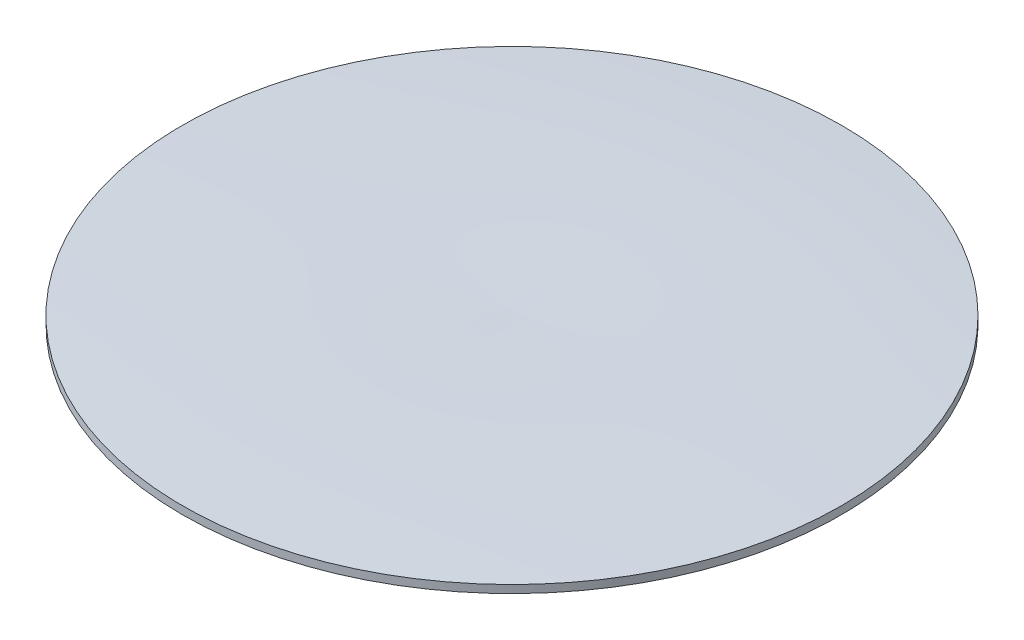
SolidWorks part; units mm, degrees
ref_plane "Front Plane" through (0, 0, 0) normal (0, 0, 1) x (1, 0, 0)
ref_plane "Top Plane" through (0, 0, 0) normal (0, 1, 0) x (1, 0, 0)
ref_plane "Right Plane" through (0, 0, 0) normal (1, 0, 0) x (0, 0, -1)
sketch "Sketch2" plane through (0, 0, 0) normal (0, 0, 1) x (1, 0, 0)
  line L0 (0, 0) -> (84, 0)
  line L1 (84, 0) -> (84, 2)
  line L2 (0, 0) -> (0, 3)
  spline S0 degree 2 poles (0, 3) (42.0472, 4.4913) (84, 2) knots 0 0 0 1 1 1
  dimension "D1" = 3
  dimension "D2" = 2
  dimension "D3" = 84
revolve "Revolve1" add sketch "Sketch2" angle 360 about L2
